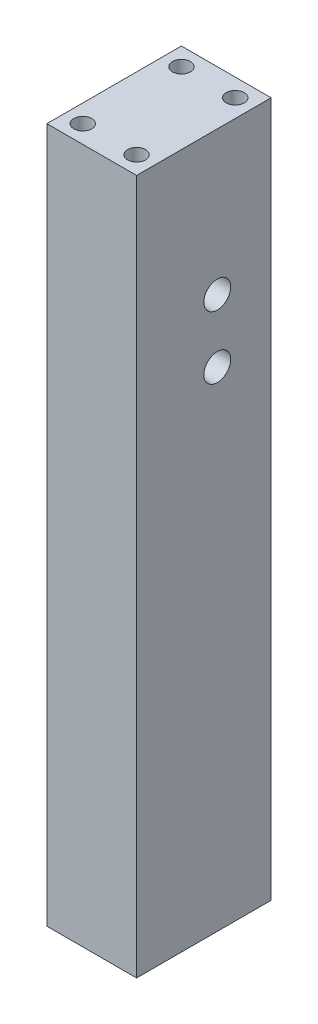
SolidWorks part; units mm, degrees
ref_plane "Front Plane" through (0, 0, 0) normal (0, 0, 1) x (1, 0, 0)
ref_plane "Top Plane" through (0, 0, 0) normal (0, 1, 0) x (1, 0, 0)
ref_plane "Right Plane" through (0, 0, 0) normal (1, 0, 0) x (0, 0, -1)
sketch "Sketch1" plane through (0, 0, 0) normal (1, 0, 0) x (0, 0, -1)
  line L1 (0, 0) -> (15, 0)
  line L2 (0, 0) -> (0, 77.5)
  line L3 (0, 77.5) -> (15, 77.5)
  line L4 (15, 0) -> (15, 77.5)
  dimension "D1" = 77.5
  dimension "D2" = 15
extrude "Boss-Extrude1" add sketch "Sketch1" along normal blind 10
ref_plane "Plane1" through (0, 77.5, 0) normal (0, 1, 0) x (1, 0, 0)
sketch "Sketch3" plane through (0, 77.5, 0) normal (0, 1, 0) x (1, 0, 0)
  line L0 (5, 15) -> (5, 0)
  line L1 (10, 15) -> (0, 15) construction
  line L2 (-5.5, 0) -> (5.5, 0) construction
  line L3 (10, 7.5) -> (0, 7.5)
  line L4 (10, 15) -> (10, 0) construction
  line L5 (0, -8.25) -> (0, 8.25) construction
  circle A0 centre (2, 13) radius 1
  circle A1 centre (8, 13) radius 1
  circle A2 centre (8, 2) radius 1
  circle A3 centre (2, 2) radius 1
  dimension "D1" = 2
  dimension "D2" = 2
  dimension "D3" = 2
extrude "Cut-Extrude1" cut sketch "Sketch3" against normal blind 10 contours A0 | A1 | A2 | A3
ref_plane "Plane2" through (0, 0, 0) normal (0, -1, 0) x (-1, 0, 0)
sketch "Sketch4" plane through (0, 0, 0) normal (0, -1, 0) x (-1, 0, 0)
  line L0 (-5, 15) -> (-5, 0)
  line L1 (-10, 15) -> (0, 15) construction
  line L2 (-5.5, 0) -> (5.5, 0) construction
  line L3 (-10, 7.5) -> (0, 7.5)
  line L4 (-10, 0) -> (-10, 15) construction
  line L5 (0, 8.25) -> (0, -8.25) construction
  circle A0 centre (-2, 2) radius 1
  circle A1 centre (-8, 2) radius 1
  circle A2 centre (-8, 13) radius 1
  circle A3 centre (-2, 13) radius 1
  dimension "D1" = 2
  dimension "D3" = 2
  dimension "D2" = 2
extrude "Cut-Extrude2" cut sketch "Sketch4" against normal blind 10 contours A1 | A2 | A3 | A0
ref_plane "Plane3" through (10, 0, 0) normal (1, 0, 0) x (0, 0, -1)
sketch "Sketch5" plane through (10, 0, 0) normal (1, 0, 0) x (0, 0, -1)
  line L0 (15, 0) -> (15, 77.5) construction
  line L1 (5.5, 77.5) -> (-5.5, 77.5) construction
  line L2 (0, 5.5) -> (0, -5.5) construction
  line L3 (0, 64.75) -> (15, 64.75)
  line L4 (0, 64.75) -> (0, 51.25)
  line L5 (0, 51.25) -> (15, 51.25)
  line L6 (15, 64.75) -> (15, 51.25)
  line L7 (0, 58) -> (15, 58)
  circle A0 centre (9, 61.5) radius 1.5
  circle A1 centre (9, 54.5) radius 1.5
  dimension "D1" = 3
  dimension "D2" = 6
  dimension "D3" = 16
  dimension "D4" = 13.5
  dimension "D5" = 12.75
extrude "Cut-Extrude3" cut sketch "Sketch5" against normal blind 5 contours A0 | A1
